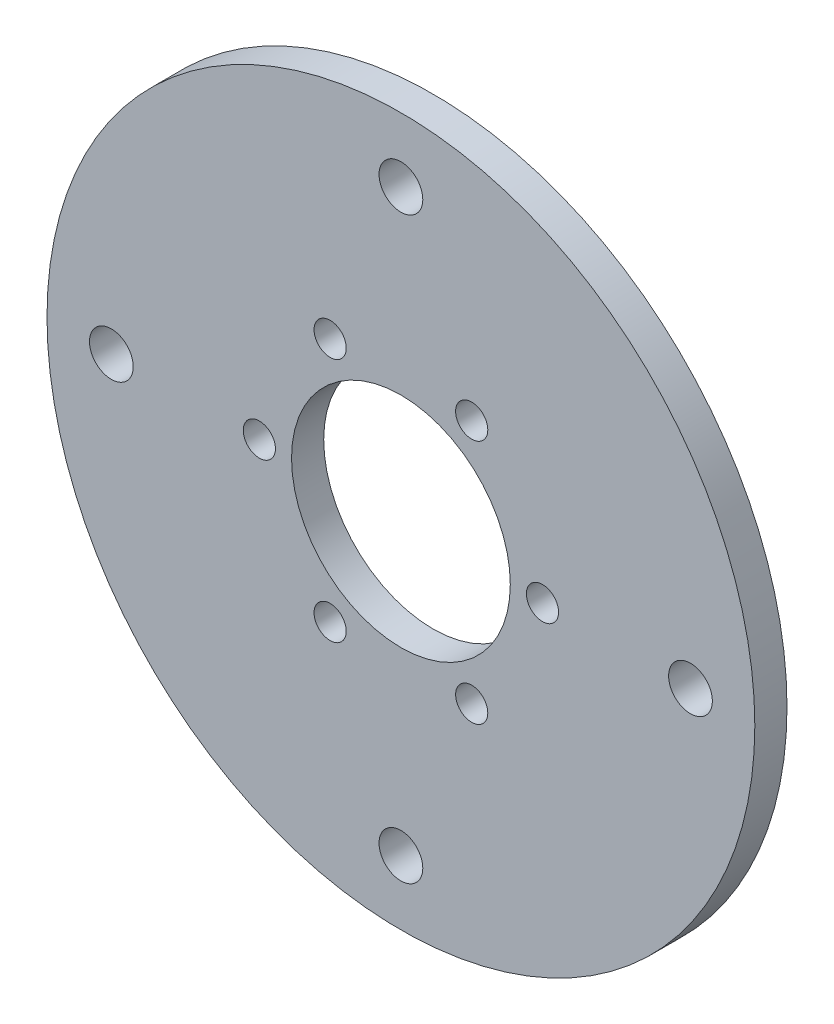
SolidWorks part; units mm, degrees
ref_plane "Plan de face" through (0, 0, 0) normal (0, 0, 1) x (1, 0, 0)
ref_plane "Plan de dessus" through (0, 0, 0) normal (0, 1, 0) x (1, 0, 0)
ref_plane "Plan de droite" through (0, 0, 0) normal (1, 0, 0) x (0, 0, -1)
sketch "Esquisse1" plane through (0, 0, 0) normal (0, 0, 1) x (1, 0, 0)
  line L0 (0, 55) -> (0, -55) construction
  line L2 (-55, 0) -> (55, 0) construction
  circle A0 centre (0, 0) radius 55
  circle A1 centre (0, 0) radius 17
  dimension "D1" = 110
  dimension "D2" = 34
extrude "Boss.-Extru.1" add sketch "Esquisse1" along normal blind 5
hole_wizard "Trou pour taraudage pour trou taraudé M8x1.252" positions "Esquisse3" profile "Esquisse2" hole size "M8x1.25" standard "Ansi Metric" end condition through all
sketch "Esquisse3" plane through (0, 0, 5) normal (0, 0, 1) x (1, 0, 0)
  circle A0 centre (0, 0) radius 55 construction
  point P0 (0, 45)
  point P12 (45, 0)
  point P13 (0, -45)
  point P14 (-45, 0)
  dimension "D1" = 45
  dimension "D2" = 4
sketch "Esquisse2" plane through (0, 45, 5) normal (1, 0, 0) x (0, -1, 0)
  line L0 (0, 0) -> (0, 5)
  line L1 (0, 5) -> (3.4, 5)
  line L2 (3.4, 5) -> (3.4, 0)
  line L5 (3.4, 0) -> (0, 0)
  line L11 (0, -6.35) -> (0, 107.95) construction
  dimension "Diamètre du perçage jusqu'au prochain" = 6.8
  dimension "Profondeur du perçage jusqu'au prochain" = 5
hole_wizard "Trou pour taraudage pour trou taraudé M6x1.02" positions "Esquisse5" profile "Esquisse4" hole size "M6x1.0" standard "Ansi Metric" end condition through all
sketch "Esquisse5" plane through (0, 0, 5) normal (0, 0, 1) x (1, 0, 0)
  line L0 (0, 0) -> (0, 58.6939) construction
  line L1 (0, 58.6939) -> (11, 19.0526) construction
  line L2 (11, 19.0526) -> (0, 0) construction
  point P0 (11, 19.0526)
  point P8 (22, 0)
  point P9 (11, -19.0526)
  point P10 (-11, -19.0526)
  point P11 (-22, 0)
  point P12 (-11, 19.0526)
  dimension "D1" = 22
  dimension "D3" = 30
  dimension "D2" = 6
sketch "Esquisse4" plane through (11, 19.0526, 5) normal (1, 0, 0) x (0, -1, 0)
  line L0 (0, 0) -> (0, 5)
  line L1 (0, 5) -> (2.5, 5)
  line L2 (2.5, 5) -> (2.5, 0)
  line L5 (2.5, 0) -> (0, 0)
  line L11 (0, -6.35) -> (0, 107.95) construction
  dimension "Diamètre du perçage jusqu'au prochain" = 5
  dimension "Profondeur du perçage jusqu'au prochain" = 5
